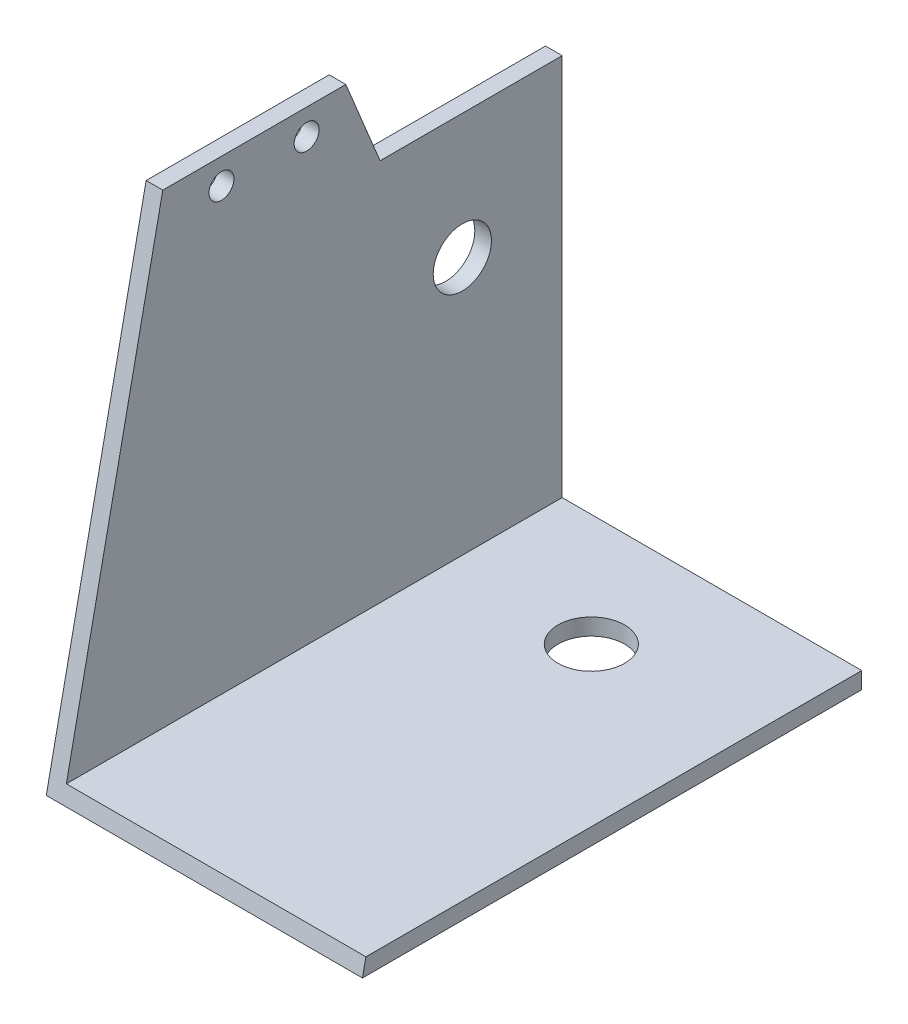
SolidWorks part; units mm, degrees
ref_plane "前视基准面" through (0, 0, 0) normal (0, 0, 1) x (1, 0, 0)
ref_plane "上视基准面" through (0, 0, 0) normal (0, 1, 0) x (1, 0, 0)
ref_plane "右视基准面" through (0, 0, 0) normal (1, 0, 0) x (0, 0, -1)
sketch "草图1" plane through (0, 0, 0) normal (0, 0, 1) x (1, 0, 0)
  line L0 (0, 58) -> (0, 0)
  line L1 (0, 0) -> (38, 0)
  line L2 (38, 0) -> (38, 2)
  line L3 (38, 2) -> (2, 2)
  line L4 (2, 2) -> (2, 58)
  line L5 (2, 58) -> (0, 58)
  dimension "D1" = 38
  dimension "D2" = 58
  dimension "D3" = 2
  dimension "D4" = 2
extrude "凸台-拉伸1" add sketch "草图1" along normal blind 60
sketch "草图2" plane through (0, 0, 0) normal (-1, 0, 0) x (0, 0, 1)
  line L0 (60, 0) -> (60, 58)
  line L1 (60, 58) -> (60, 0) construction
  line L2 (60, 58) -> (48, 58)
  line L3 (60, 58) -> (0, 58) construction
  line L4 (48, 58) -> (60, 0)
  line L5 (26, 58) -> (21.8846, 48)
  line L6 (21.8846, 48) -> (0, 48)
  line L7 (0, 58) -> (0, 0) construction
  line L8 (0, 48) -> (0, 58)
  line L9 (0, 58) -> (26, 58)
  line L10 (60, 0) -> (0, 0) construction
  circle A0 centre (30.7109, 54.9127) radius 1.5
  circle A1 centre (40.9484, 54.9127) radius 1.5
  circle A2 centre (12, 33) radius 3.5
  dimension "D4" = 3
  dimension "D5" = 7
  dimension "D6" = 12
  dimension "D7" = 33
  dimension "D1" = 12
  dimension "D2" = 22
  dimension "D3" = 10
extrude "切除-拉伸1" cut sketch "草图2" against normal through all
sketch "草图3" plane through (0, 0, 0) normal (0, -1, 0) x (1, 0, 0)
  line L0 (19, 0) -> (19, 33.4126) construction
  line L1 (0, 0) -> (38, 0) construction
  circle A0 centre (19, 13.5) radius 4
  point P6 (0, 0)
  dimension "D1" = 8
  dimension "D2" = 13.5
extrude "切除-拉伸2" cut sketch "草图3" against normal blind 50
